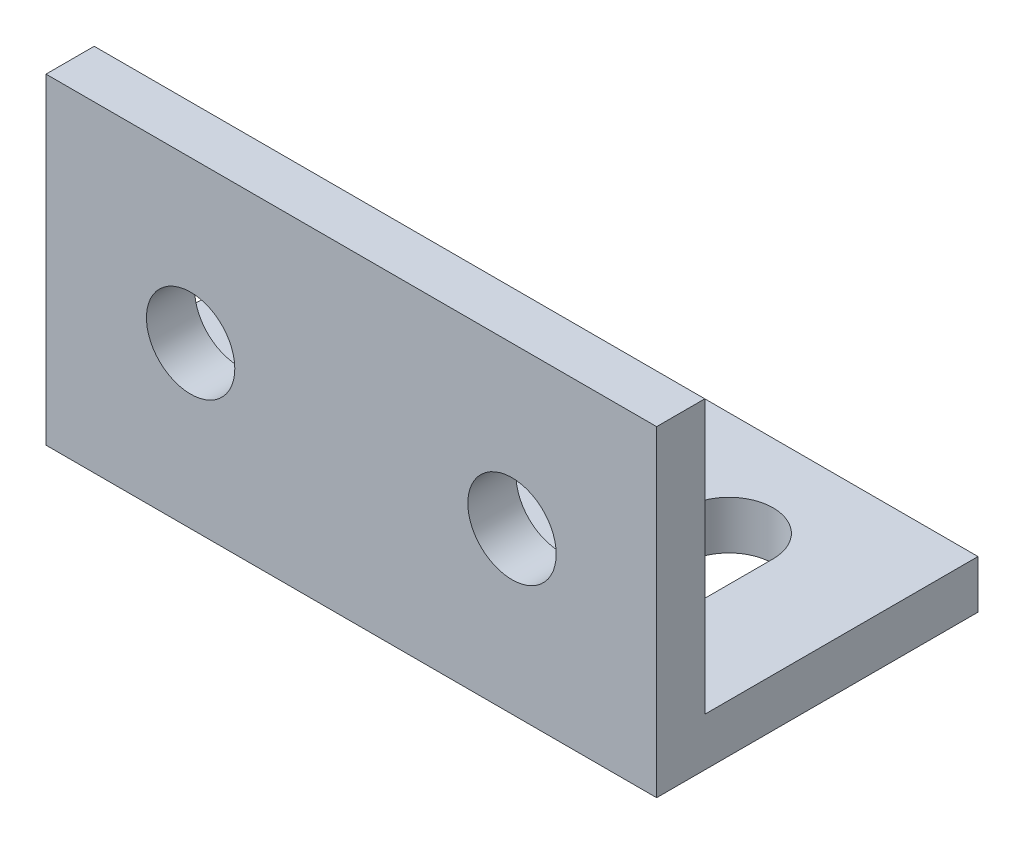
SolidWorks part; units mm, degrees
ref_plane "前视基准面" through (0, 0, 0) normal (0, 0, 1) x (1, 0, 0)
ref_plane "上视基准面" through (0, 0, 0) normal (0, 1, 0) x (1, 0, 0)
ref_plane "右视基准面" through (0, 0, 0) normal (1, 0, 0) x (0, 0, -1)
sketch "草图1" plane through (0, 0, 0) normal (1, 0, 0) x (0, 0, -1)
  line L0 (0, 0) -> (20, 0)
  line L1 (20, 0) -> (20, 3)
  line L2 (20, 3) -> (3, 3)
  line L3 (3, 3) -> (3, 20)
  line L4 (3, 20) -> (0, 20)
  line L5 (0, 20) -> (0, 0)
  dimension "D1" = 3
  dimension "D2" = 3
  dimension "D3" = 20
  dimension "D4" = 20
extrude "凸台-拉伸1" add sketch "草图1" along normal blind 38
sketch "草图2" plane through (0, 0, 0) normal (0, 0, 1) x (1, 0, 0)
  line L0 (0, 20) -> (0, 0) construction
  line L1 (38, 20) -> (0, 20) construction
  circle A0 centre (9, 10) radius 2.75
  circle A1 centre (29, 10) radius 2.75
  dimension "D1" = 5.5
  dimension "D2" = 9
  dimension "D3" = 10
  dimension "D4" = 2
extrude "切除-拉伸1" cut sketch "草图2" against normal through all
sketch "草图3" plane through (0, 0, 0) normal (0, -1, 0) x (1, 0, 0)
  line L0 (38, -20) -> (0, -20) construction
  line L1 (6.25, -3.75) -> (11.75, -3.75) construction
  line L2 (6.25, -3.75) -> (6.25, -16.25) construction
  line L3 (6.25, -16.25) -> (11.75, -16.25) construction
  line L4 (11.75, -3.75) -> (11.75, -16.25) construction
  line L5 (6.25, -3.75) -> (11.75, -16.25) construction
  line L6 (6.25, -16.25) -> (11.75, -3.75) construction
  line L7 (0, 0) -> (0, -20) construction
  line L8 (6.25, -13.5) -> (6.25, -6.5)
  line L9 (11.75, -13.5) -> (11.75, -6.5)
  line L10 (26.25, -13.5) -> (26.25, -6.5)
  line L11 (31.75, -13.5) -> (31.75, -6.5)
  arc A0 (11.75, -6.5) -> (6.25, -6.5) centre (9, -6.5) ccw
  arc A1 (6.25, -13.5) -> (11.75, -13.5) centre (9, -13.5) ccw
  arc A2 (31.75, -6.5) -> (26.25, -6.5) centre (29, -6.5) ccw
  arc A3 (26.25, -13.5) -> (31.75, -13.5) centre (29, -13.5) ccw
  point P0 (9, -10)
  dimension "D5" = 5.5
  dimension "D6" = 5.5
  dimension "D1" = 5.5
  dimension "D2" = 12.5
  dimension "D3" = 10
  dimension "D4" = 9
  dimension "D7" = 2
extrude "切除-拉伸2" cut sketch "草图3" against normal through all
